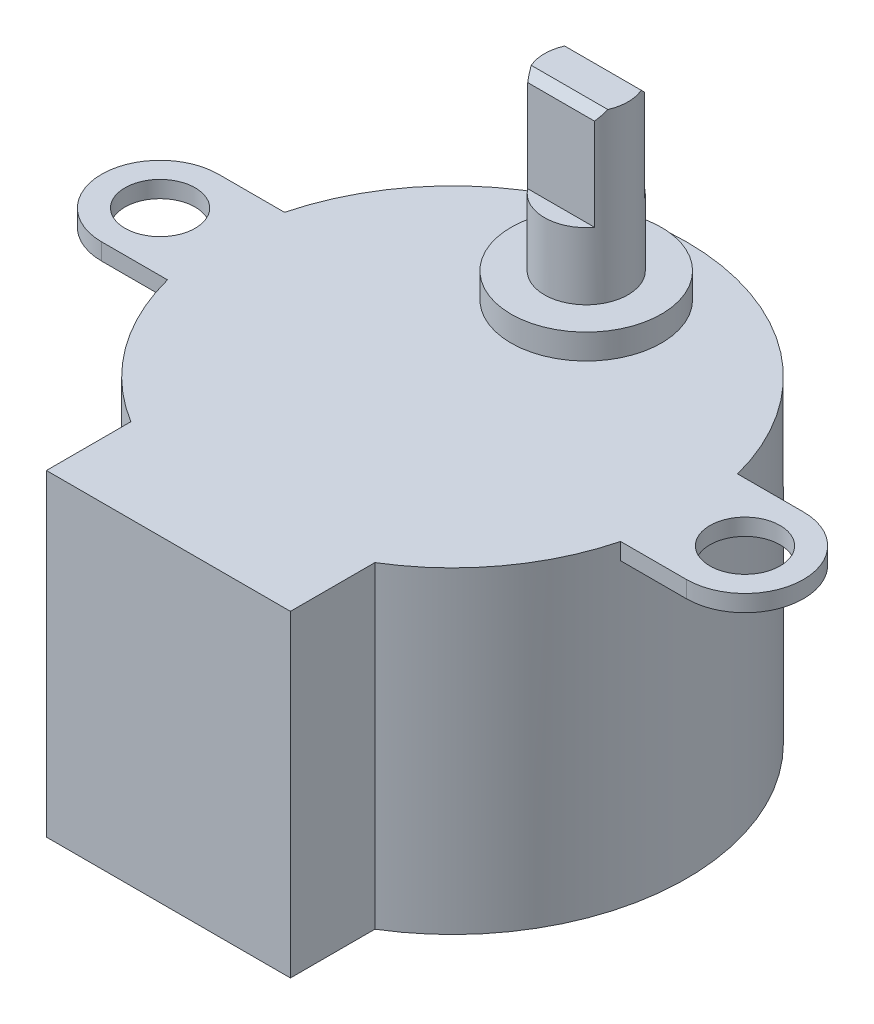
SolidWorks part; units mm, degrees
ref_plane "Front Plane" through (0, 0, 0) normal (0, 0, 1) x (1, 0, 0)
ref_plane "Top Plane" through (0, 0, 0) normal (0, 1, 0) x (1, 0, 0)
ref_plane "Right Plane" through (0, 0, 0) normal (1, 0, 0) x (0, 0, -1)
sketch "Sketch1" plane through (0, 0, 0) normal (0, 1, 0) x (1, 0, 0)
  circle A0 centre (0, 0) radius 14
  dimension "D1" = 28
extrude "Boss-Extrude1" add sketch "Sketch1" along normal blind 19
sketch "Sketch2" plane through (0, 19, 0) normal (0, 1, 0) x (1, 0, 0)
  line L0 (0, 0) -> (17.5, 0) construction
  line L1 (0, 0) -> (-17.5, 0) construction
  line L2 (-17.5, 3.5) -> (-13.5554, 3.5)
  line L3 (-17.5, -3.5) -> (-13.5554, -3.5)
  line L4 (0, 0) -> (0, 14) construction
  line L5 (17.5, -3.5) -> (13.5554, -3.5)
  line L6 (17.5, 3.5) -> (13.5554, 3.5)
  circle A0 centre (-17.5, 0) radius 2.1
  arc A2 (-17.5, 3.5) -> (-17.5, -3.5) centre (-17.5, 0) ccw
  circle A3 centre (0, 0) radius 14 construction
  arc A4 (17.5, 3.5) -> (17.5, -3.5) centre (17.5, 0) cw
  circle A5 centre (17.5, 0) radius 2.1
  arc A6 (-13.5554, 3.5) -> (-13.5554, -3.5) centre (0, 0) ccw
  arc A7 (13.5554, 3.5) -> (13.5554, -3.5) centre (0, 0) cw
  dimension "D2" = 7
  dimension "D3" = 4.2
  dimension "D1" = 35
extrude "Boss-Extrude2" add sketch "Sketch2" against normal blind 1
sketch "Sketch3" plane through (0, 19, 0) normal (0, 1, 0) x (1, 0, 0)
  line L0 (0, 8) -> (0, 0) construction
  circle A0 centre (0, 8) radius 4.5
  point P2 (0, 6.2842)
  dimension "D2" = 9
  dimension "D1" = 8
extrude "Boss-Extrude3" add sketch "Sketch3" along normal blind 1.5
sketch "Sketch4" plane through (0, 20.5, 0) normal (0, 1, 0) x (1, 0, 0)
  circle A0 centre (0, 8) radius 2.5
  dimension "D1" = 5
extrude "Boss-Extrude4" add sketch "Sketch4" along normal blind 10
sketch "Sketch5" plane through (0, 30.5, 0) normal (0, 1, 0) x (1, 0, 0)
  line L0 (-2.5, 8) -> (2.5, 8) construction
  line L1 (-2, 9.5) -> (2, 9.5)
  line L2 (-2, 6.5) -> (2, 6.5)
  line L3 (0, 9.5) -> (0, 6.5) construction
  circle A0 centre (0, 8) radius 2.5 construction
  circle A1 centre (0, 8) radius 2.5 construction
  arc A2 (-2, 9.5) -> (2, 9.5) centre (0, 8) cw
  arc A3 (-2, 6.5) -> (2, 6.5) centre (0, 8) ccw
  dimension "D1" = 3
extrude "Cut-Extrude1" cut sketch "Sketch5" against normal blind 6
chamfer "Chamfer1" distance 0.5 angle 45 2 edges at (0, 30.5, -6.5) (0, 30.5, -9.5)
sketch "Sketch6" plane through (0, 19, 0) normal (0, 1, 0) x (1, 0, 0)
  line L0 (0, 0) -> (0, -17) construction
  line L1 (-7.3, -17) -> (7.3, -17)
  line L2 (-7.3, -17) -> (-7.3, -11.9461)
  line L3 (7.3, -11.9461) -> (7.3, -17)
  arc A0 (-13.5554, -3.5) -> (13.5554, -3.5) centre (0, 0) ccw construction
  arc A2 (-7.3, -11.9461) -> (7.3, -11.9461) centre (0, 0) ccw
  point P6 (0, -17)
  dimension "D1" = 17
  dimension "D2" = 14.6
extrude "Boss-Extrude5" add sketch "Sketch6" against normal up to surface (19 mm away) up to face at (0, 0, 14)
